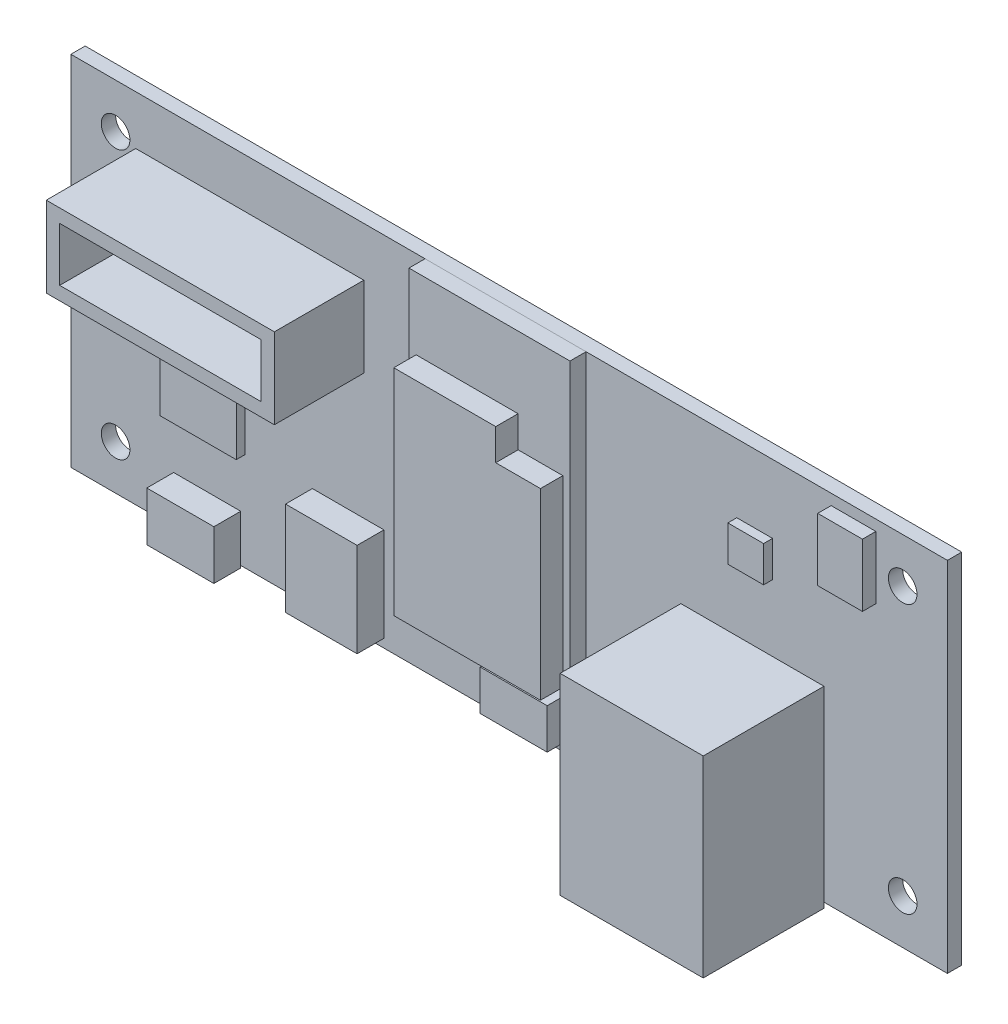
SolidWorks part; units mm, degrees
ref_plane "Front Plane" through (0, 0, 0) normal (0, 0, 1) x (1, 0, 0)
ref_plane "Top Plane" through (0, 0, 0) normal (0, 1, 0) x (1, 0, 0)
ref_plane "Right Plane" through (0, 0, 0) normal (1, 0, 0) x (0, 0, -1)
sketch "Sketch1" plane through (0, 0, 0) normal (0, 0, 1) x (1, 0, 0)
  line L1 (-49, 20) -> (49, 20)
  line L2 (-49, 20) -> (-49, -20)
  line L3 (-49, -20) -> (49, -20)
  line L4 (49, 20) -> (49, -20)
  line L5 (-49, 20) -> (49, -20) construction
  line L6 (-49, -20) -> (49, 20) construction
  point P0 (0, 0)
  dimension "D1" = 98
  dimension "D2" = 40
extrude "Boss-Extrude1" add sketch "Sketch1" along normal blind 1.6
sketch "Sketch2" plane through (0, 0, 1.6) normal (0, 0, 1) x (1, 0, 0)
  line L0 (-49, 20) -> (-49, -20) construction
  line L1 (-49, -20) -> (49, -20) construction
  line L2 (-5.6894, 0) -> (6.6859, 0) construction
  line L3 (0, 4.4796) -> (0, -4.8064) construction
  circle A0 centre (-44, -15) radius 1.6
  circle A1 centre (-44, 15) radius 1.6
  circle A2 centre (44, 15) radius 1.6
  circle A3 centre (44, -15) radius 1.6
  dimension "D1" = 3.2
  dimension "D3" = 5
  dimension "D2" = 5
extrude "Cut-Extrude1" cut sketch "Sketch2" against normal through all both and the other way through all
sketch "Sketch3" plane through (0, 0, 1.6) normal (0, 0, 1) x (1, 0, 0)
  line L0 (-49, -20) -> (49, -20) construction
  line L1 (-41.75, 14.5) -> (-16.25, 14.5)
  line L2 (-41.75, 14.5) -> (-41.75, 5.5)
  line L3 (-41.75, 5.5) -> (-16.25, 5.5)
  line L4 (-16.25, 14.5) -> (-16.25, 5.5)
  line L5 (-41.75, 14.5) -> (-16.25, 5.5) construction
  line L6 (-41.75, 5.5) -> (-16.25, 14.5) construction
  line L7 (-49, 20) -> (-49, -20) construction
  point P0 (-29, 10)
  dimension "D1" = 30
  dimension "D2" = 20
  dimension "D3" = 9
  dimension "D4" = 25.5
extrude "Boss-Extrude2" add sketch "Sketch3" along normal blind 10 separate body
shell "Shell1" thickness 1.5
sketch "Sketch4" plane through (0, 0, 1.6) normal (0, 0, 1) x (1, 0, 0)
  line L0 (-49, 20) -> (-49, -20) construction
  line L1 (-38.01, -0.51) -> (-29.51, -0.51)
  line L2 (-38.01, -0.51) -> (-38.01, -9.01)
  line L3 (-38.01, -9.01) -> (-29.51, -9.01)
  line L4 (-29.51, -0.51) -> (-29.51, -9.01)
  line L5 (-38.01, -0.51) -> (-29.51, -9.01) construction
  line L6 (-38.01, -9.01) -> (-29.51, -0.51) construction
  line L8 (-49, -20) -> (49, -20) construction
  point P0 (-33.76, -4.76)
  point P7 (0, 0)
  point P9 (-34.9251, -20)
  dimension "D1" = 15.24
  dimension "D2" = 15.24
  dimension "D3" = 8.5
  dimension "D4" = 8.5
extrude "Boss-Extrude3" add sketch "Sketch4" along normal blind 1 separate body
sketch "Sketch5" plane through (0, 0, 1.6) normal (0, 0, 1) x (1, 0, 0)
  line L0 (-49, 20) -> (-49, -20) construction
  line L1 (-37.51, -14.75) -> (-30.01, -14.75)
  line L2 (-37.51, -14.75) -> (-37.51, -20.25)
  line L3 (-37.51, -20.25) -> (-30.01, -20.25)
  line L4 (-30.01, -14.75) -> (-30.01, -20.25)
  line L5 (-37.51, -14.75) -> (-30.01, -20.25) construction
  line L6 (-37.51, -20.25) -> (-30.01, -14.75) construction
  line L7 (-49, -20) -> (49, -20) construction
  point P0 (-33.76, -17.5)
  dimension "D1" = 15.24
  dimension "D2" = 7.5
  dimension "D3" = 5.5
  dimension "D4" = 0.25
extrude "Boss-Extrude4" add sketch "Sketch5" along normal blind 3 separate body
sketch "Sketch6" plane through (0, 0, 1.6) normal (0, 0, 1) x (1, 0, 0)
  line L0 (-49, -20) -> (49, -20) construction
  line L1 (-22, -8.55) -> (-14, -8.55)
  line L2 (-22, -8.55) -> (-22, -19.05)
  line L3 (-22, -19.05) -> (-14, -19.05)
  line L4 (-14, -8.55) -> (-14, -19.05)
  line L5 (-22, -8.55) -> (-14, -19.05) construction
  line L6 (-22, -19.05) -> (-14, -8.55) construction
  line L7 (-49, 20) -> (-49, -20) construction
  point P0 (-18, -13.8)
  dimension "D1" = 6.2
  dimension "D2" = 31
  dimension "D3" = 10.5
  dimension "D4" = 8
extrude "Boss-Extrude5" add sketch "Sketch6" along normal blind 3 separate body
sketch "Sketch7" plane through (0, 0, 1.6) normal (0, 0, 1) x (1, 0, 0)
  line L0 (-49, 20) -> (-49, -20) construction
  line L1 (-9.4, 20) -> (8.6, 20)
  line L2 (-9.4, 20) -> (-9.4, -12)
  line L3 (-9.4, -12) -> (8.6, -12)
  line L4 (8.6, 20) -> (8.6, -12)
  line L5 (-9.4, 20) -> (8.6, -12) construction
  line L6 (-9.4, -12) -> (8.6, 20) construction
  line L8 (-49, -20) -> (49, -20) construction
  point P0 (-0.4, 4)
  dimension "D1" = 48.6
  dimension "D2" = 24
  dimension "D3" = 32
  dimension "D4" = 18
extrude "Boss-Extrude6" add sketch "Sketch7" along normal blind 1.8 separate body
sketch "Sketch8" plane through (0, 0, 3.4) normal (0, 0, 1) x (1, 0, 0)
  line L0 (-8.6, 12) -> (-8.6, -12)
  line L1 (-9.4, -12) -> (8.6, -12) construction
  line L2 (-8.6, -12) -> (7.8, -12)
  line L3 (7.8, -12) -> (7.8, 8.5)
  line L4 (7.8, 8.5) -> (2.8, 8.5)
  line L5 (2.8, 8.5) -> (2.8, 12)
  line L6 (2.8, 12) -> (-8.6, 12)
  line L7 (-9.4, 20) -> (-9.4, -12) construction
  line L8 (8.6, -12) -> (8.6, 20) construction
  dimension "D1" = 24
  dimension "D2" = 0.8
  dimension "D3" = 0.8
  dimension "D4" = 5
  dimension "D5" = 3.5
extrude "Boss-Extrude7" add sketch "Sketch8" along normal blind 2.5 separate body
sketch "Sketch9" plane through (0, 0, 1.6) normal (0, 0, 1) x (1, 0, 0)
  line L0 (-49, -20) -> (49, -20) construction
  line L1 (0.25, -12.95) -> (7.75, -12.95)
  line L2 (0.25, -12.95) -> (0.25, -17.45)
  line L3 (0.25, -17.45) -> (7.75, -17.45)
  line L4 (7.75, -12.95) -> (7.75, -17.45)
  line L5 (0.25, -12.95) -> (7.75, -17.45) construction
  line L6 (0.25, -17.45) -> (7.75, -12.95) construction
  line L8 (-49, 20) -> (-49, -20) construction
  point P0 (4, -15.2)
  point P7 (0, 0)
  point P9 (-49, -12.7877)
  dimension "D1" = 4.8
  dimension "D2" = 53
  dimension "D3" = 7.5
  dimension "D4" = 4.5
extrude "Boss-Extrude8" add sketch "Sketch9" along normal blind 3.5
sketch "Sketch10" plane through (0, 0, 1.6) normal (0, 0, 1) x (1, 0, 0)
  line L0 (-49, -20) -> (49, -20) construction
  line L1 (19.2, 0.91) -> (35.2, 0.91)
  line L2 (19.2, 0.91) -> (19.2, -20.59)
  line L3 (19.2, -20.59) -> (35.2, -20.59)
  line L4 (35.2, 0.91) -> (35.2, -20.59)
  line L5 (19.2, 0.91) -> (35.2, -20.59) construction
  line L6 (19.2, -20.59) -> (35.2, 0.91) construction
  line L7 (-49, 20) -> (-49, -20) construction
  point P0 (27.2, -9.84)
  dimension "D1" = 10.16
  dimension "D2" = 76.2
  dimension "D3" = 16
  dimension "D4" = 21.5
extrude "Boss-Extrude9" add sketch "Sketch10" along normal blind 13.5 separate body
sketch "Sketch11" plane through (0, -20.59, 0) normal (0, -1, 0) x (1, 0, 0)
  line L0 (35.2, 15.1) -> (35.2, 1.6) construction
  line L1 (21.2, 12.6) -> (33.2, 12.6)
  line L2 (21.2, 12.6) -> (21.2, 5.5)
  line L3 (21.2, 5.5) -> (33.2, 5.5)
  line L4 (33.2, 12.6) -> (33.2, 5.5)
  line L5 (21.2, 12.6) -> (33.2, 5.5) construction
  line L6 (21.2, 5.5) -> (33.2, 12.6) construction
  line L7 (19.2, 15.1) -> (19.2, 1.6) construction
  line L8 (19.2, 15.1) -> (35.2, 15.1) construction
  line L9 (-49, 0) -> (49, 0) construction
  line L11 (24.2, 5.5) -> (30.2, 5.5)
  line L12 (24.2, 5.5) -> (24.2, 4.5)
  line L13 (24.2, 4.5) -> (30.2, 4.5)
  line L14 (30.2, 5.5) -> (30.2, 4.5)
  line L15 (25.2, 4.5) -> (29.2, 4.5)
  line L16 (25.2, 4.5) -> (25.2, 3.5)
  line L17 (25.2, 3.5) -> (29.2, 3.5)
  line L18 (29.2, 4.5) -> (29.2, 3.5)
  line L19 (25.2, 4.5) -> (29.2, 3.5) construction
  line L20 (25.2, 3.5) -> (29.2, 4.5) construction
  point P0 (27.2, 9.05)
  point P17 (27.2, 4)
  dimension "D1" = 2
  dimension "D2" = 2
  dimension "D3" = 2.5
  dimension "D4" = 5.5
  dimension "D5" = 6
  dimension "D6" = 3
  dimension "D7" = 1
  dimension "D8" = 1
  dimension "D9" = 0
  dimension "D10" = 3
  dimension "D11" = 4
extrude "Cut-Extrude2" cut sketch "Sketch11" against normal blind 10 contours L4 L1 L2 L3 | L14 L3 L12 L13 | L18 L13 L16 L17
sketch "Sketch12" plane through (0, 0, 1.6) normal (0, 0, 1) x (1, 0, 0)
  line L0 (-49, -20) -> (49, -20) construction
  line L1 (25.45, 12.35) -> (29.45, 12.35)
  line L2 (25.45, 12.35) -> (25.45, 8.35)
  line L3 (25.45, 8.35) -> (29.45, 8.35)
  line L4 (29.45, 12.35) -> (29.45, 8.35)
  line L5 (25.45, 12.35) -> (29.45, 8.35) construction
  line L6 (25.45, 8.35) -> (29.45, 12.35) construction
  line L7 (-49, 20) -> (-49, -20) construction
  point P0 (27.45, 10.35)
  dimension "D1" = 4
  dimension "D2" = 4
  dimension "D3" = 30.35
  dimension "D4" = 76.45
extrude "Boss-Extrude10" add sketch "Sketch12" along normal blind 1 separate body
sketch "Sketch13" plane through (0, 0, 1.6) normal (0, 0, 1) x (1, 0, 0)
  line L0 (-49, -20) -> (49, -20) construction
  line L1 (36, 18.8) -> (41, 18.8)
  line L2 (36, 18.8) -> (36, 11.8)
  line L3 (36, 11.8) -> (41, 11.8)
  line L4 (41, 18.8) -> (41, 11.8)
  line L5 (36, 18.8) -> (41, 11.8) construction
  line L6 (36, 11.8) -> (41, 18.8) construction
  line L8 (-49, 20) -> (-49, -20) construction
  point P0 (38.5, 15.3)
  point P7 (0, 0)
  point P9 (-49, -3.1399)
  dimension "D1" = 5
  dimension "D2" = 7
  dimension "D3" = 35.3
  dimension "D4" = 87.5
extrude "Boss-Extrude11" add sketch "Sketch13" along normal blind 1.5 separate body
